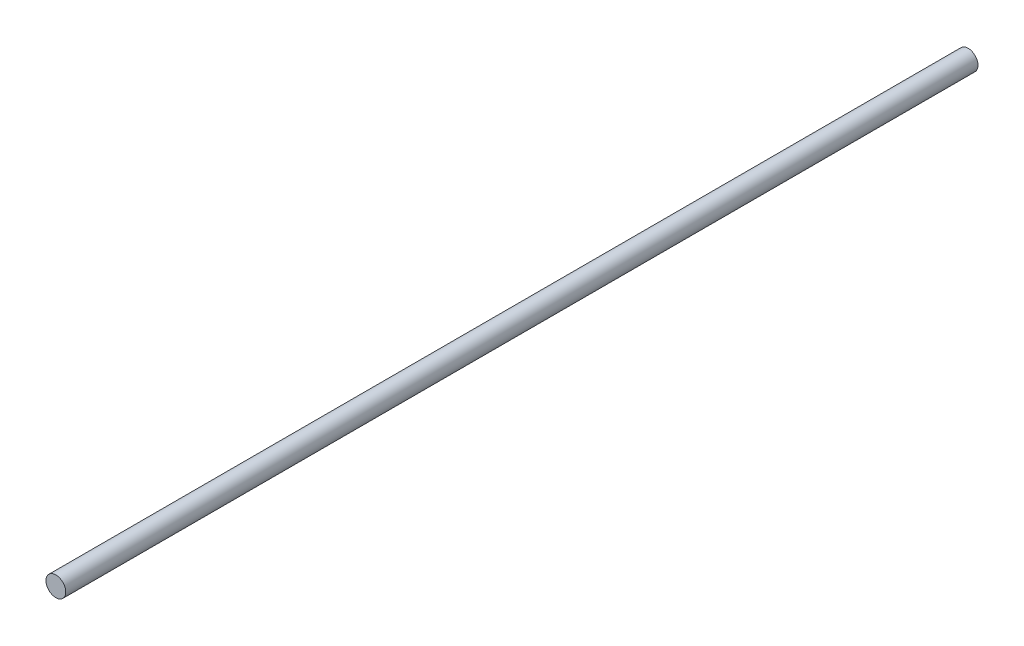
SolidWorks part; units mm, degrees
ref_plane "Front Plane" through (0, 0, 0) normal (0, 0, 1) x (1, 0, 0)
ref_plane "Top Plane" through (0, 0, 0) normal (0, 1, 0) x (1, 0, 0)
ref_plane "Right Plane" through (0, 0, 0) normal (1, 0, 0) x (0, 0, -1)
sketch "Sketch1" plane through (0, 0, 0) normal (0, 0, 1) x (1, 0, 0)
  circle A0 centre (0, 0) radius 3.302
  dimension "D1" = 6.604
extrude "Boss-Extrude1" add sketch "Sketch1" along normal blind 304.8
